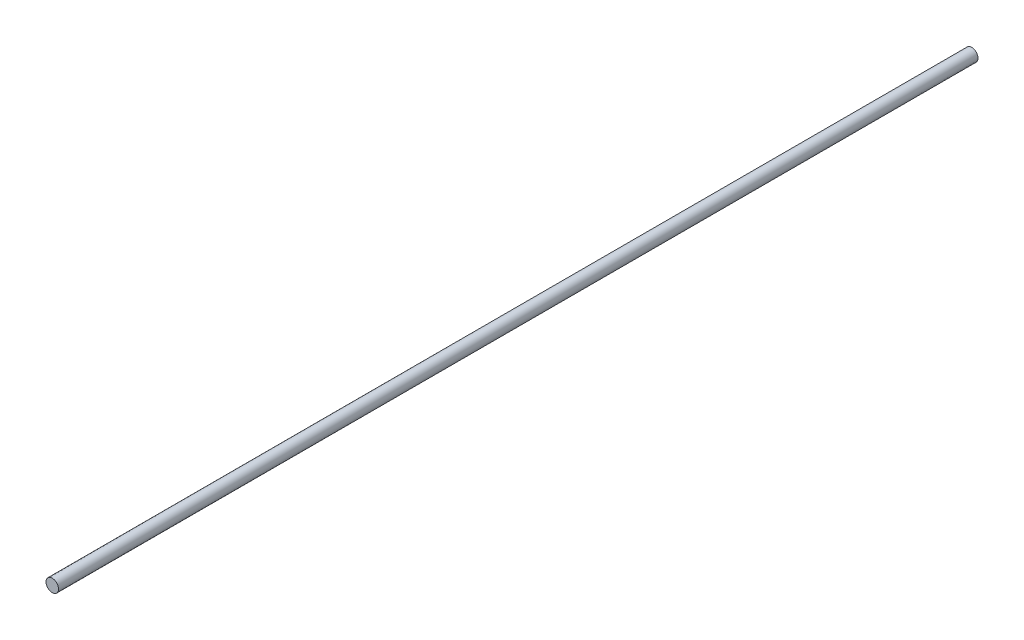
SolidWorks part; units mm, degrees
ref_plane "Plan de face" through (0, 0, 0) normal (0, 0, 1) x (1, 0, 0)
ref_plane "Plan de dessus" through (0, 0, 0) normal (0, 1, 0) x (1, 0, 0)
ref_plane "Plan de droite" through (0, 0, 0) normal (1, 0, 0) x (0, 0, -1)
sketch "Esquisse1" plane through (0, 0, 0) normal (0, 0, 1) x (1, 0, 0)
  circle A0 centre (0, 0) radius 1.5
  dimension "D1" = 3
extrude "Boss.-Extru.1" add sketch "Esquisse1" along normal blind 220
